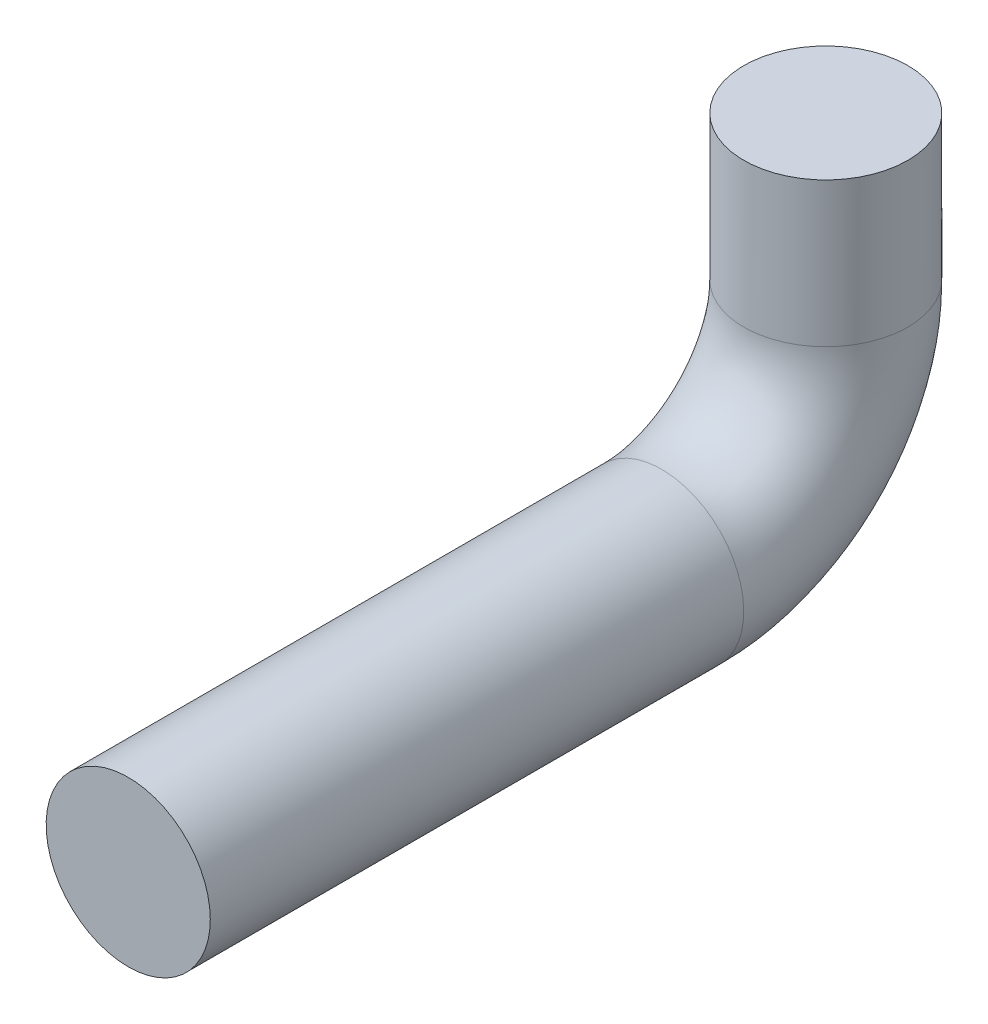
SolidWorks part; units mm, degrees
ref_plane "Front Plane" through (0, 0, 0) normal (0, 0, 1) x (1, 0, 0)
ref_plane "Top Plane" through (0, 0, 0) normal (0, 1, 0) x (1, 0, 0)
ref_plane "Right Plane" through (0, 0, 0) normal (1, 0, 0) x (0, 0, -1)
sketch "Sketch2" plane through (0, 0, 0) normal (1, 0, 0) x (0, 0, -1)
  line L0 (0, 0) -> (0, -22.352)
  line L1 (-25.4, -47.752) -> (-107.95, -47.752)
  arc A0 (-25.4, -47.752) -> (0, -22.352) centre (-25.4, -22.352) ccw
  point P6 (0, -47.752)
  dimension "D3" = 25.4
  dimension "D1" = 47.752
  dimension "D2" = 107.95
ref_plane "Plane1" through (0, 0, 107.95) normal (0, 0, 1) x (1, 0, 0)
sketch "Sketch3" plane through (0, 0, 107.95) normal (0, 0, 1) x (1, 0, 0)
  circle A0 centre (0, -47.752) radius 12.7
  dimension "D1" = 25.4
sweep "Sweep1" add profiles "Sketch3" path "Sketch2"
